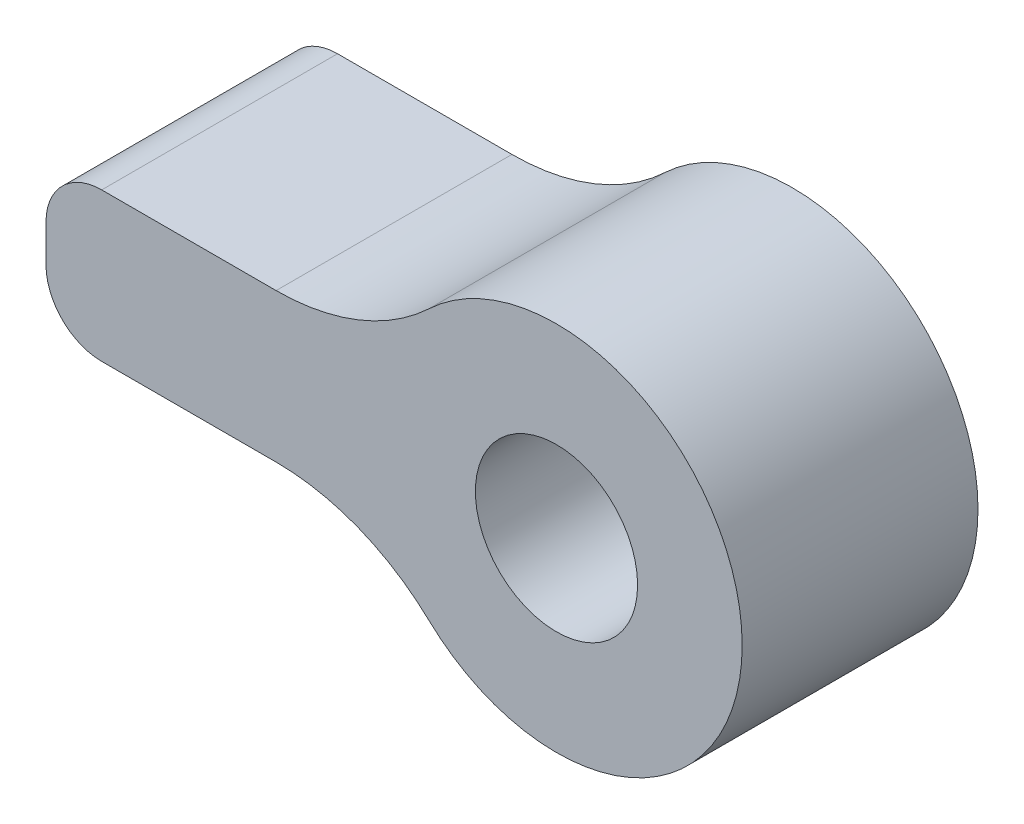
SolidWorks part; units mm, degrees
ref_plane "Front Plane" through (0, 0, 0) normal (0, 0, 1) x (1, 0, 0)
ref_plane "Top Plane" through (0, 0, 0) normal (0, 1, 0) x (1, 0, 0)
ref_plane "Right Plane" through (0, 0, 0) normal (1, 0, 0) x (0, 0, -1)
sketch "Sketch1" plane through (0, 0, 0) normal (0, 0, 1) x (1, 0, 0)
  line L53 (97.5193, 20.5548) -> (97.6173, 20.5548)
  line L58 (97.5193, 18.5548) -> (97.6173, 18.5548)
  line L66 (95.2693, 20.5548) -> (97.5193, 20.5548)
  line L71 (94.5193, 19.8048) -> (94.5193, 19.3048)
  line L73 (95.2693, 18.5548) -> (97.5193, 18.5548)
  arc A154 (99.6764, 17.7367) -> (99.6764, 21.373) centre (101.3922, 19.5548) ccw
  arc A155 (94.5193, 19.3048) -> (95.2693, 18.5548) centre (95.2693, 19.3048) ccw
  arc A156 (94.5193, 19.8048) -> (95.2693, 20.5548) centre (95.2693, 19.8048) cw
  arc A157 (97.6173, 18.5548) -> (99.6764, 17.7367) centre (97.6173, 15.5548) cw
  arc A166 (97.6173, 20.5548) -> (99.6764, 21.373) centre (97.6173, 23.5548) ccw
  circle A167 centre (101.3922, 19.5548) radius 1.0922
  point P6 (33.4759, 5.4562)
  point P22 (-18.296, 4.9144)
  point P24 (31.704, 4.9144)
  point P79 (34.204, 10.9144)
  point P80 (14.204, 10.9144)
  point P81 (14.204, -9.0856)
  point P82 (-0.796, -9.0856)
  point P83 (-0.796, 10.9144)
  point P85 (-20.796, 10.9144)
  point P109 (9.593, -9.8856)
  point P112 (6.704, -9.8856)
  point P126 (-16.5241, 5.4562)
extrude "Boss-Extrude1" add sketch "Sketch1" along normal blind 3.175
